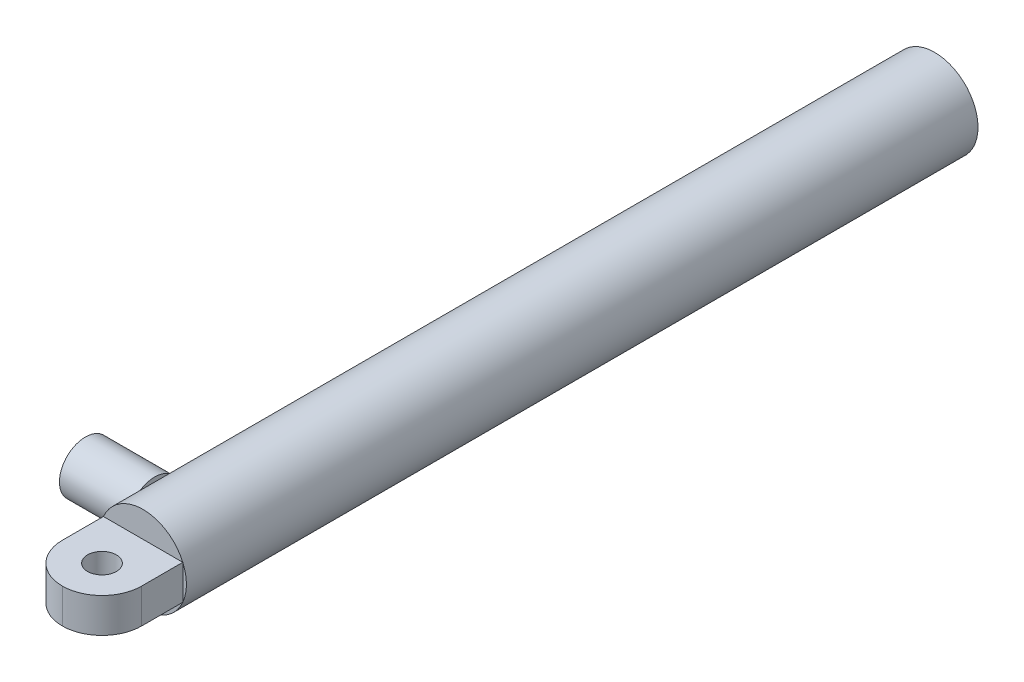
SolidWorks part; units mm, degrees
ref_plane "Front Plane" through (0, 0, 0) normal (0, 0, 1) x (1, 0, 0)
ref_plane "Top Plane" through (0, 0, 0) normal (0, 1, 0) x (1, 0, 0)
ref_plane "Right Plane" through (0, 0, 0) normal (1, 0, 0) x (0, 0, -1)
sketch "Sketch1" plane through (0, 0, 0) normal (0, 0, 1) x (1, 0, 0)
  circle A0 centre (0, 0) radius 37.5
  circle A1 centre (0, 0) radius 17.5
  dimension "D1" = 75
  dimension "D2" = 35
extrude "Boss-Extrude1" add sketch "Sketch1" along normal blind 664
sketch "Sketch5" plane through (0, 0, 664) normal (0, 0, 1) x (1, 0, 0)
  circle A0 centre (0, 0) radius 37.5
  circle A1 centre (0, 0) radius 37.5 construction
extrude "Boss-Extrude2" add sketch "Sketch5" along normal blind 22
sketch "Sketch8" plane through (0, 0, 686) normal (0, 0, 1) x (1, 0, 0)
  line L0 (41.25, 0) -> (-41.25, 0) construction
  line L1 (-34.3693, -15) -> (34.3693, -15)
  line L2 (-34.3693, -15) -> (-34.3693, 0)
  line L3 (-34.3693, 0) -> (34.3693, 0)
  line L4 (34.3693, -15) -> (34.3693, 0)
  circle A0 centre (0, 0) radius 37.5 construction
  dimension "D1" = 15
extrude "Boss-Extrude3" add sketch "Sketch8" along normal blind 70
mirror "Mirror1" about plane through (-34.3693, 0, 756) normal (0, -1, 0) of "Boss-Extrude3"
fillet "Fillet1" radius 34.36 2 edges at (34.3693, 0, 756) (-34.3693, 0, 756)
sketch "Sketch9" plane through (0, 15, 0) normal (0, 1, 0) x (1, 0, 0)
  circle A0 centre (0, -721.64) radius 12.5
  arc A1 (-34.3693, -721.64) -> (-0.0093, -756) centre (-0.0093, -721.64) ccw construction
  dimension "D2" = 25
  dimension "D1" = 0
extrude "Cut-Extrude1" cut sketch "Sketch9" against normal mid plane 200
sketch "Sketch10" plane through (-34.3693, 0, 0) normal (-1, 0, 0) x (0, 0, 1)
  line L0 (41.25, 0) -> (-41.25, 0) construction
  line L1 (721.64, -15) -> (721.64, 15) construction
  circle A0 centre (641.64, 0) radius 22.5
  dimension "D1" = 45
  dimension "D2" = 80
extrude "Boss-Extrude4" add sketch "Sketch10" along normal blind 60
